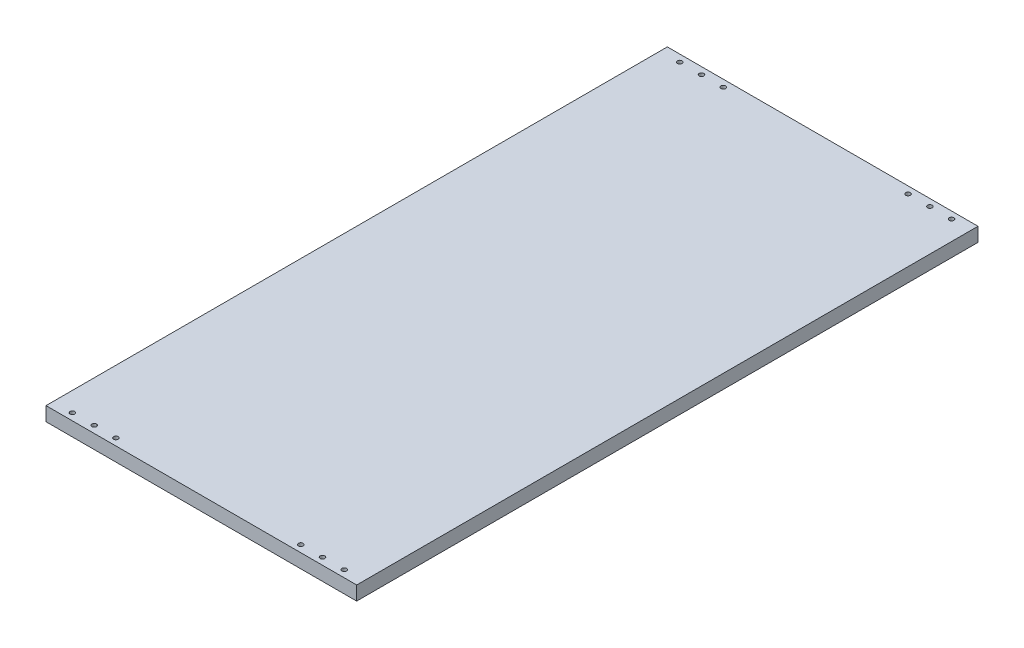
SolidWorks part; units mm, degrees
ref_plane "Спереди" through (0, 0, 0) normal (0, 0, 1) x (1, 0, 0)
ref_plane "Сверху" through (0, 0, 0) normal (0, 1, 0) x (1, 0, 0)
ref_plane "Справа" through (0, 0, 0) normal (1, 0, 0) x (0, 0, -1)
sketch "Эскиз1" plane through (0, 0, 0) normal (0, 1, 0) x (1, 0, 0)
  line L1 (0, 0) -> (400, 0)
  line L2 (0, 0) -> (0, 800)
  line L3 (0, 800) -> (400, 800)
  line L4 (400, 0) -> (400, 800)
extrude "Бобышка-Вытянуть1" add sketch "Эскиз1" along normal blind 18
sketch "Эскиз2" plane through (0, 18, 0) normal (0, 1, 0) x (1, 0, 0)
  line L0 (0, 400) -> (472.9857, 400) construction
  line L1 (0, 800) -> (0, 0) construction
  line L2 (200, 800) -> (200, -34.8514) construction
  line L3 (400, 800) -> (0, 800) construction
  circle A0 centre (25, 9) radius 3
  circle A1 centre (53, 9) radius 3
  circle A2 centre (81, 9) radius 3
  circle A12 centre (319, 9) radius 3
  circle A13 centre (347, 9) radius 3
  circle A14 centre (375, 9) radius 3
  circle A15 centre (375, 791) radius 3
  circle A16 centre (347, 791) radius 3
  circle A17 centre (319, 791) radius 3
  circle A18 centre (81, 791) radius 3
  circle A19 centre (53, 791) radius 3
  circle A20 centre (25, 791) radius 3
  dimension "D1" = 3
extrude "Вырез-Вытянуть1" cut sketch "Эскиз2" against normal blind 9
